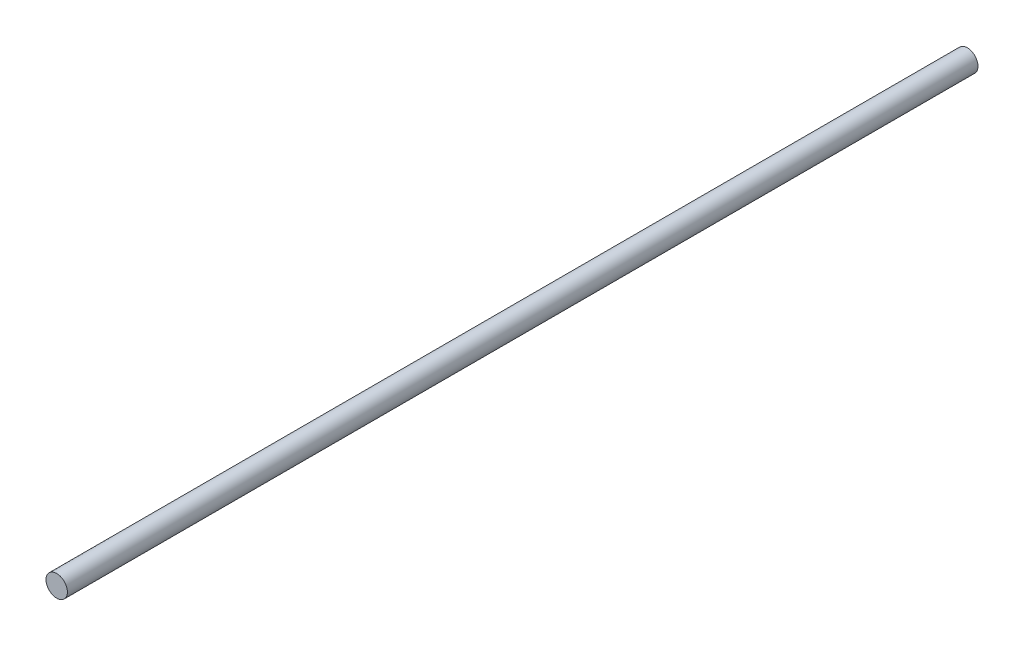
SolidWorks part; units mm, degrees
ref_plane "Front Plane" through (0, 0, 0) normal (0, 0, 1) x (1, 0, 0)
ref_plane "Top Plane" through (0, 0, 0) normal (0, 1, 0) x (1, 0, 0)
ref_plane "Right Plane" through (0, 0, 0) normal (1, 0, 0) x (0, 0, -1)
sketch "Sketch1" plane through (0, 0, 0) normal (0, 0, 1) x (1, 0, 0)
  circle A0 centre (0, 0) radius 4
  dimension "D1" = 8
extrude "Boss-Extrude1" add sketch "Sketch1" along normal blind 340
